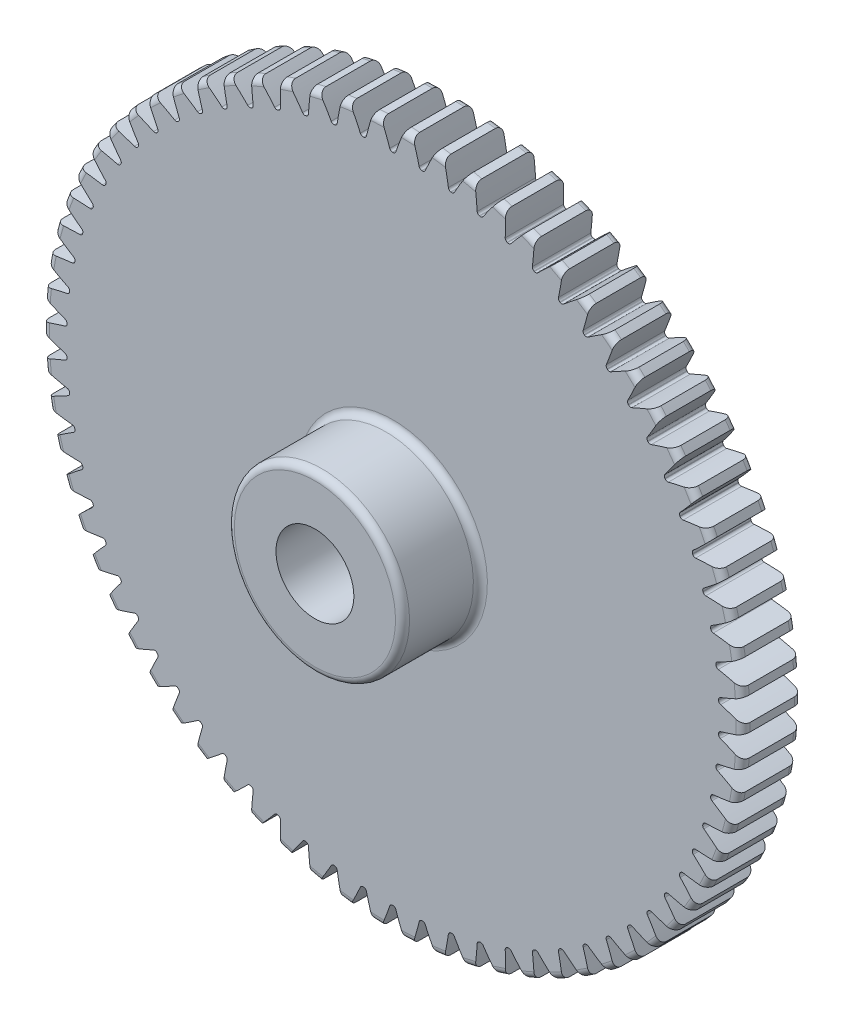
SolidWorks part; units mm, degrees
material "Delrin 2700 NC010, Low Viscosity Acetal Copolymer (SS)"
ref_plane "Front Plane" through (0, 0, 0) normal (0, 0, 1) x (1, 0, 0)
ref_plane "Top Plane" through (0, 0, 0) normal (0, 1, 0) x (1, 0, 0)
ref_plane "Right Plane" through (0, 0, 0) normal (1, 0, 0) x (0, 0, -1)
sketch "Sketch1" plane through (0, 0, 0) normal (0, 0, 1) x (1, 0, 0)
  line L0 (-889, 0) -> (889, 0) construction
  circle A0 centre (0, 0) radius 36 construction
  circle A1 centre (0, 0) radius 35 construction
  circle A2 centre (0, 0) radius 33.5 construction
  circle A3 centre (0, 0) radius 9 construction
  circle A4 centre (0, 0) radius 4 construction
  dimension "D2" = 1
  dimension "D3" = 2.5
  dimension "D1" = 2.5
sketch "Sketch2" plane through (0, 0, 0) normal (1, 0, 0) x (0, 0, -1)
  line L0 (0, 0) -> (-6, 0) construction
  line L1 (-6, 0) -> (-14, 0) construction
  dimension "Overall Width" = 14
  dimension "Face Width" = 6
sketch "Sketch4" plane through (0, 0, 0) normal (1, 0, 0) x (0, 0, -1)
  line L0 (-14, 4) -> (-14, 9)
  line L1 (-14, 9) -> (-6, 9)
  line L2 (-6, 9) -> (-6, 36)
  line L3 (-6, 36) -> (0, 36)
  line L4 (0, 36) -> (0, 4)
  line L5 (-6, 9) -> (-6, 0) construction
  line L6 (0, 36) -> (0, -36) construction
  line L7 (-6, 9) -> (0, 9) construction
  line L12 (-14, 4) -> (0, 4)
revolve "Revolve1" add sketch "Sketch4" angle 360 about L1
fillet "Fillet2" radius 0.72 4 edges at (0, 9, 14) (0, 9, 6) (0, 36, 6) (0, 36, 0)
sketch "Sketch7" plane through (0, 0, 6) normal (0, 0, 1) x (1, 0, 0)
  line L0 (0, 0) -> (0, 36) construction
  line L1 (0.7853, 34.9912) -> (1.1709, 35.981) construction
  line L3 (1.6151, 35.9638) -> (1.5703, 34.9648) construction
  line L4 (1.5703, 34.9648) -> (1.503, 33.4663) construction
  line L5 (0, 0) -> (1.503, 33.4663) construction
  line L6 (0.7853, 34.9912) -> (0, 0) construction
  line L7 (0.7853, 34.9912) -> (0.8078, 35.9909) construction
  line L8 (0.7853, 34.9912) -> (0, 0) construction
  circle A0 centre (0, 0) radius 36 construction
  arc A1 (-0.0282, 33.5) -> (0.0282, 33.5) centre (0, 0) cw
  circle A2 centre (0, 0) radius 33.5 construction
  arc A3 (-0.7853, 34.9912) -> (0.7853, 34.9912) centre (0, 0) cw construction
  circle A4 centre (0, 0) radius 35 construction
  arc A5 (2.0418, 35.942) -> (1.1882, 35.9804) centre (0, 0) ccw construction
  arc A6 (0.7853, 34.9912) -> (2.3544, 34.9207) centre (0, 0) cw construction
  arc A7 (-1.1882, 35.9804) -> (1.1882, 35.9804) centre (0, 0) cw
  arc A8 (0.312, 33.7021) -> (1.1882, 35.9804) centre (33.3977, 22.2855) cw
  arc A9 (-0.312, 33.7021) -> (-1.1882, 35.9804) centre (-33.3977, 22.2855) ccw
  arc A10 (-0.0282, 33.5) -> (-0.312, 33.7021) centre (-0.0284, 33.8) cw
  arc A11 (0.0282, 33.5) -> (0.312, 33.7021) centre (0.0284, 33.8) ccw
  point P26 (-0.2427, 33.4991)
  point P29 (0.2427, 33.4991)
  dimension "D4" = 0.3
  dimension "D5" = 35
  dimension "D3" = 20
  dimension "D1" = 3.1416
  dimension "D2" = 1.5708
extrude "Cut-Extrude2" cut sketch "Sketch7" against normal through all
pattern_circular "CirPattern1" count 70 over 360 about axis through (0, 0, 0) along (0, 0, 1) of "Cut-Extrude2"
equation "\"D1@Sketch1\"=2.5*(\"Pitch Dia.@Sketch1\"/\"Number of Teeth@Sketch1\")"
equation "\"D1@CirPattern1\"=\"Number of Teeth@Sketch1\""
equation "\"D1@Fillet2\"=\"OD@Sketch1\"*.01"
equation "\"D1@Sketch7\"=3.14159*(\"Pitch Dia.@Sketch1\"/\"Number of Teeth@Sketch1\")"
equation "\"D2@Sketch7\"=\"D1@Sketch7\"/2"
equation "\"D4@Sketch7\"=\"D1@Sketch7\"*.0955"
equation "\"D5@Sketch7\"=\"Pitch Dia.@Sketch1\"/2"
